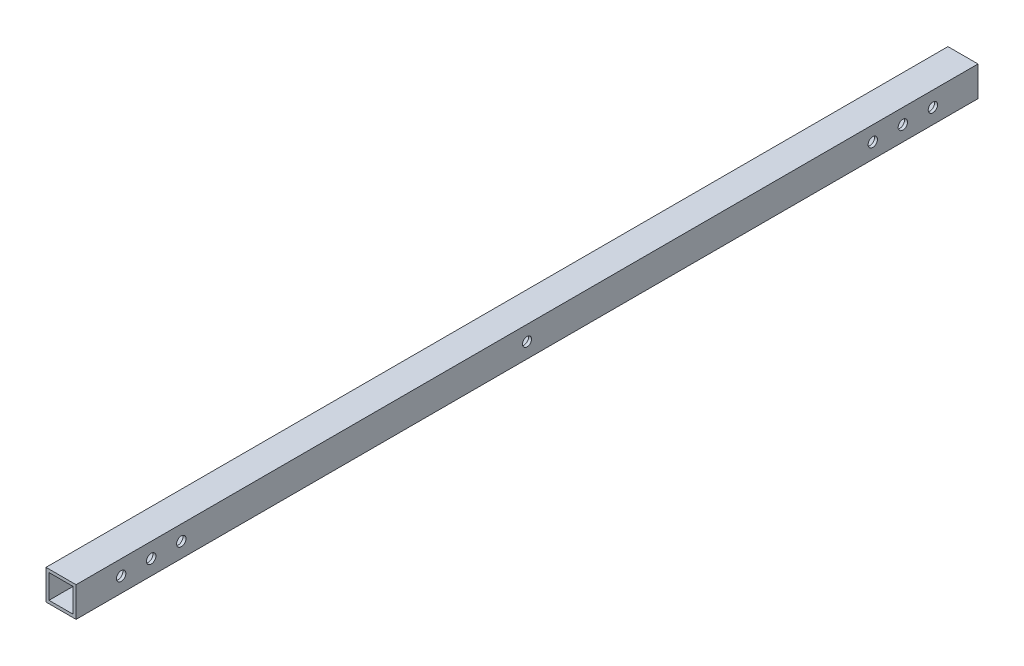
SolidWorks part; units mm, degrees
ref_plane "前视基准面" through (0, 0, 0) normal (0, 0, 1) x (1, 0, 0)
ref_plane "上视基准面" through (0, 0, 0) normal (0, 1, 0) x (1, 0, 0)
ref_plane "右视基准面" through (0, 0, 0) normal (1, 0, 0) x (0, 0, -1)
sketch "草图1" plane through (0, 0, 0) normal (1, 0, 0) x (0, 0, -1)
  line L0 (95.0272, 5.1351) -> (95.0272, -26.6956) construction
  line L1 (-54.9728, 5.1351) -> (245.0272, 5.1351)
  line L2 (-54.9728, 5.1351) -> (-54.9728, -4.8649)
  line L3 (-54.9728, -4.8649) -> (245.0272, -4.8649)
  line L4 (245.0272, 5.1351) -> (245.0272, -4.8649)
  circle A0 centre (-39.9728, 0.1351) radius 1.5584
  circle A1 centre (-29.9728, 0.1351) radius 1.5584
  circle A2 centre (-19.9728, 0.1351) radius 1.5584
  circle A3 centre (210.0272, 0.1351) radius 1.5584
  circle A4 centre (220.0272, 0.1351) radius 1.5584
  circle A5 centre (230.0272, 0.1351) radius 1.5584
  dimension "D1" = 10
  dimension "D2" = 300
  dimension "D3" = 15
  dimension "D4" = 5
  dimension "D5" = 2
  dimension "D6" = 2
extrude "凸台-拉伸4" add sketch "草图1" along normal blind 10 contours L3 L4 L1 L2
sketch "草图5" plane through (10, 0, 0) normal (1, 0, 0) x (0, 0, -1)
  line L0 (-54.9728, 5.1351) -> (245.0272, 5.1351) construction
  line L3 (245.0272, 5.1351) -> (245.0272, -4.8649) construction
  circle A0 centre (95.0272, 0.1351) radius 1.5
  point P6 (152.724, -33.9182)
  point P7 (245.0272, 3.2652)
  dimension "D3" = 3
  dimension "D1" = 5
  dimension "D2" = 150
extrude "切除-拉伸1" cut sketch "草图5" against normal blind 10 contours A0
sketch "草图9" plane through (0, 0, 54.9728) normal (0, 0, 1) x (1, 0, 0)
  line L0 (10, 5.1351) -> (0, 5.1351) construction
  line L1 (1, 4.1351) -> (9, 4.1351)
  line L2 (1, 4.1351) -> (1, -3.8649)
  line L3 (1, -3.8649) -> (9, -3.8649)
  line L4 (9, 4.1351) -> (9, -3.8649)
  line L5 (0, 5.1351) -> (0, -4.8649) construction
  dimension "D1" = 8
  dimension "D2" = 8
  dimension "D3" = 1
  dimension "D4" = 1
extrude "切除-拉伸4" cut sketch "草图9" against normal blind 300
